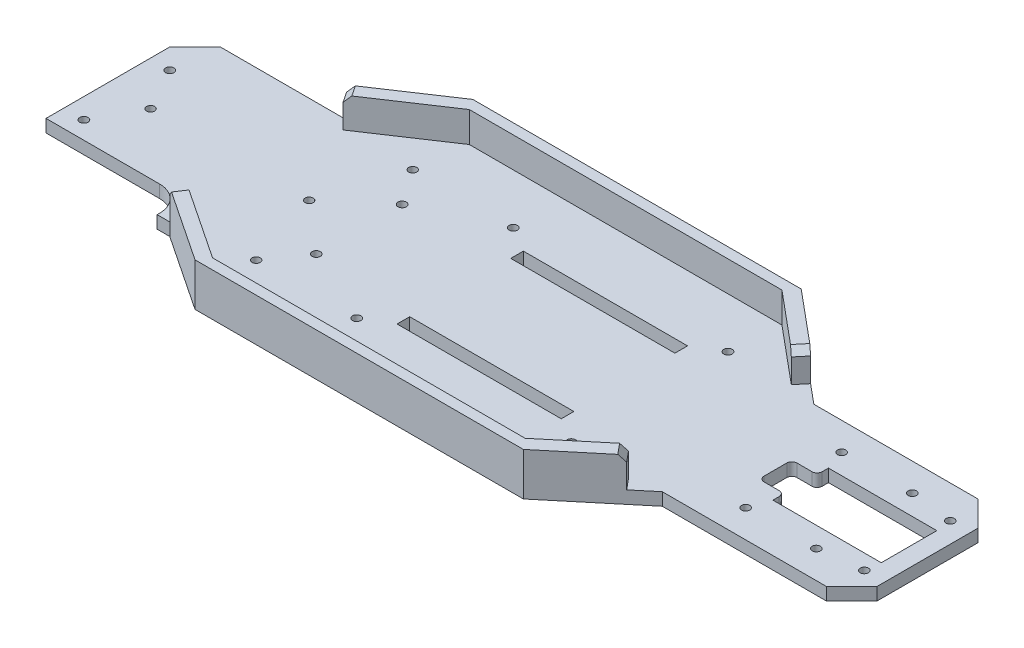
SolidWorks part; units mm, degrees
material "PETG - Polymaker"
ref_plane "Front Plane" through (0, 0, 0) normal (0, 0, 1) x (1, 0, 0)
ref_plane "Top Plane" through (0, 0, 0) normal (0, 1, 0) x (1, 0, 0)
ref_plane "Right Plane" through (0, 0, 0) normal (1, 0, 0) x (0, 0, -1)
sketch "Sketch1" plane through (0, 0, 0) normal (0, 1, 0) x (1, 0, 0)
  line L0 (-235.1499, 0) -> (235.1499, 0) construction
  line L1 (0, 0) -> (0, 52596.8311) construction
  line L2 (-95, 35) -> (-65, 55)
  line L3 (-65, 55) -> (65, 55)
  line L4 (-95, 35) -> (-155, 35)
  line L5 (-155, 35) -> (-155, -35)
  line L6 (-65, -55) -> (65, -55)
  line L7 (-95, -35) -> (-65, -55)
  line L8 (-95, -35) -> (-155, -35)
  line L9 (65, 55) -> (95, 30)
  line L10 (95, 30) -> (170, 30)
  line L11 (170, 30) -> (170, -30)
  line L12 (95, -30) -> (170, -30)
  line L13 (65, -55) -> (95, -30)
  point P3 (0, 0)
  point P10 (-80, 45)
  point P15 (-80, -45)
  point P18 (-155, 0)
  point P19 (0, -55)
  point P20 (0, 55)
  point P23 (170, 0)
  dimension "D1" = 55
  dimension "D2" = 70
  dimension "D3" = 30
  dimension "D4" = 60
  dimension "D5" = 130
  dimension "D6" = 75
  dimension "D7" = 60
  dimension "D8" = 30
  dimension "D9" = 110
extrude "Boss-Extrude1" add sketch "Sketch1" along normal blind 5
sketch "Sketch3" plane through (0, 5, 0) normal (0, 1, 0) x (1, 0, 0)
  line L0 (0, 0) -> (50000, 0) construction
  line L1 (0, 0) -> (0, 50000) construction
  line L2 (0, 55) -> (-65, 55)
  line L3 (65, 55) -> (-65, 55) construction
  line L4 (-65, 55) -> (-95, 35)
  line L5 (-95, 35) -> (-92.2265, 30.8397)
  line L6 (-92.2265, 30.8397) -> (-62.2265, 50.8397)
  line L7 (-62.2265, 50.8397) -> (0, 50.8397)
  line L8 (-65, 55) -> (-62.2265, 50.8397) construction
  line L9 (0, 55) -> (65, 55)
  line L10 (65, 55) -> (87.3178, 36.4018)
  line L11 (87.3178, 36.4018) -> (83.8509, 32.2416)
  line L12 (83.8509, 32.2416) -> (61.5331, 50.8397)
  line L13 (61.5331, 50.8397) -> (0, 50.8397)
  line L14 (61.5331, 50.8397) -> (65, 55) construction
  line L15 (61.5331, -50.8397) -> (65, -55) construction
  line L16 (-65, -55) -> (-62.2265, -50.8397) construction
  line L27 (-65, 55) -> (-95, 35) construction
  line L28 (95, 30) -> (65, 55) construction
  line L29 (61.5331, -50.8397) -> (0, -50.8397)
  line L30 (83.8509, -32.2416) -> (61.5331, -50.8397)
  line L31 (87.3178, -36.4018) -> (83.8509, -32.2416)
  line L32 (65, -55) -> (87.3178, -36.4018)
  line L33 (0, -55) -> (65, -55)
  line L34 (-62.2265, -50.8397) -> (0, -50.8397)
  line L35 (-92.2265, -30.8397) -> (-62.2265, -50.8397)
  line L36 (-95, -35) -> (-92.2265, -30.8397)
  line L37 (-65, -55) -> (-95, -35)
  line L38 (0, -55) -> (-65, -55)
  dimension "D1" = 5
  dimension "D2" = 0
  dimension "D3" = 10
extrude "Chassis-Walls1" add sketch "Sketch3" along normal blind 12
chamfer "Chamfer1" distance 10 angle 45 2 edges at (-155, 2.5, -35) (-155, 2.5, 35)
chamfer "Chamfer2" distance 10 angle 45 2 edges at (170, 2.5, -30) (170, 2.5, 30)
chamfer "Chamfer3" distance 2.5 angle 45 4 edges at (-93.6132, 17, -32.9199) (85.5843, 17, -34.3217) (-93.6132, 17, 32.9199) (85.5843, 17, 34.3217)
sketch "Sketch4" plane through (0, 0, 0) normal (0, -1, 0) x (1, 0, 0)
  line L0 (0, 0) -> (50000, 0) construction
  line L1 (-147, 17) -> (-55, 17) construction
  line L2 (-155, -25) -> (-155, 25) construction
  circle A0 centre (-147, 17) radius 1.65
  circle A1 centre (-55, 17) radius 1.65
  circle A2 centre (-55, -17) radius 1.65
  circle A3 centre (-147, -17) radius 1.65
  circle A4 centre (-25, 31) radius 1.65
  circle A5 centre (60, 31) radius 1.65
  circle A6 centre (60, -31) radius 1.65
  circle A7 centre (-25, -31) radius 1.65
  dimension "D1" = 3.3
  dimension "D2" = 3.3
  dimension "D6" = 3.3
  dimension "D8" = 3.3
  dimension "D3" = 8
  dimension "D4" = 92
  dimension "D5" = 34
  dimension "D7" = 30
  dimension "D9" = 85
  dimension "D10" = 62
extrude "Cut-Extrude1" cut sketch "Sketch4" against normal blind 10
sketch "Sketch5" plane through (0, 5, 0) normal (0, 1, 0) x (1, 0, 0)
  line L0 (-155, -24) -> (-100, -24)
  line L1 (-155, 25) -> (-155, -25) construction
  line L2 (-100, -24) -> (-100, -35)
  line L3 (-145, -35) -> (-95, -35) construction
  line L4 (-100, -35) -> (-155, -35)
  line L5 (-155, -35) -> (-155, -24)
  dimension "D1" = 55
  dimension "D2" = 11
extrude "Cut-Extrude2" cut sketch "Sketch5" against normal blind 10
sketch "Sketch6" plane through (0, 5, 0) normal (0, 1, 0) x (1, 0, 0)
  line L0 (0, 0) -> (50000, 0) construction
  line L1 (60, 31) -> (-25, 31) construction
  line L2 (17.5, 30.75) -> (17.5, 50030.75) construction
  line L3 (-15, -20) -> (50, -25) construction
  line L4 (-15, 25) -> (50, 25)
  line L5 (-15, 25) -> (-15, 20)
  line L6 (-15, 20) -> (50, 20)
  line L7 (50, 25) -> (50, 20)
  line L8 (-15, 25) -> (50, 20) construction
  line L9 (-15, 20) -> (50, 25) construction
  line L10 (-15, -25) -> (50, -20) construction
  line L11 (50, -25) -> (50, -20)
  line L12 (-15, -20) -> (50, -20)
  line L13 (-15, -25) -> (-15, -20)
  line L14 (-15, -25) -> (50, -25)
  point P9 (17.5, 31)
  point P10 (17.5, 22.5)
  point P19 (17.5, -22.5)
  dimension "D1" = 5
  dimension "D2" = 65
  dimension "D3" = 20
extrude "Cut-Extrude3" cut sketch "Sketch6" against normal through all
fillet "Fillet1" radius 10 1 edges at (-100, 2.5, 24)
sketch "Sketch7" plane through (0, 5, 0) normal (0, 1, 0) x (1, 0, 0)
  line L0 (175, 0) -> (50175, 0) construction
  line L1 (170, -20) -> (170, 20) construction
  line L3 (120.8, 10) -> (161.7, 10) construction
  line L4 (120.8, 10) -> (120.8, -10) construction
  line L5 (120.8, -10) -> (161.7, -10) construction
  line L6 (161.7, 10) -> (161.7, -10) construction
  line L7 (120.8, 10) -> (161.7, -10) construction
  line L8 (120.8, -10) -> (161.7, 10) construction
  line L9 (119.8, 11) -> (162.7, 11)
  line L10 (119.8, 11) -> (119.8, -11)
  line L11 (119.8, -11) -> (162.7, -11)
  line L12 (162.7, 11) -> (162.7, -11)
  line L13 (119.8, 11) -> (162.7, -11) construction
  line L14 (119.8, -11) -> (162.7, 11) construction
  point P4 (170, 0)
  point P5 (141.25, 0)
  point P10 (141.25, 0)
  dimension "D1" = 20
  dimension "D2" = 40.9
  dimension "D3" = 1
  dimension "D4" = 1
  dimension "D5" = 8.3
extrude "Cut-Extrude4" cut sketch "Sketch7" against normal through all
sketch "Sketch9" plane through (0, 5, 0) normal (0, 1, 0) x (1, 0, 0)
  circle A0 centre (117, -19) radius 1.625
  circle A1 centre (145, -19) radius 1.625
  circle A2 centre (162, -17) radius 1.625
  dimension "D1" = 3.25
  dimension "D2" = 3.25
  dimension "D3" = 3.25
extrude "Cut-Extrude5" cut sketch "Sketch9" against normal through all
mirror "Mirror1" about plane through (0, 0, 0) normal (0, 0, 1) of "Cut-Extrude5"
sketch "Sketch10" plane through (0, 5, 0) normal (0, 1, 0) x (1, 0, 0)
  line L0 (124.8, 0) -> (50124.8, 0) construction
  line L1 (119.8, 11) -> (119.8, -11) construction
  line L2 (119.8, 6.5) -> (109.8, 6.5)
  line L3 (109.8, 6.5) -> (109.8, -6.5)
  line L4 (119.8, 6.5) -> (119.8, -6.5)
  line L5 (119.8, -6.5) -> (109.8, -6.5)
  point P4 (119.8, 0)
  point P10 (119.8, 0)
  point P11 (109.8, 0)
  dimension "D1" = 13
  dimension "D2" = 10
extrude "Servo-Cable-Cutout" cut sketch "Sketch10" against normal blind 10
fillet "Fillet2" radius 2 4 edges at (119.8, 2.5, -6.5) (119.8, 2.5, 6.5) (109.8, 2.5, 6.5) (109.8, 2.5, -6.5)
sketch "Sketch11" plane through (0, 5, 0) normal (0, 1, 0) x (1, 0, 0)
  line L0 (-153, 11.5) -> (-153, -11.5) construction
  line L1 (-153, 0) -> (-122.2, 0) construction
  line L2 (-122.2, -11.5) -> (-122.2, 11.5) construction
  line L3 (-122.2, 0) -> (-47.5, 0) construction
  line L4 (-47.5, -12.0003) -> (-47.5, 9.9997) construction
  line L5 (-79.8, 9.5) -> (-79.8, -9.5) construction
  line L6 (-74.8, 0) -> (-74.8, 50000) construction
  line L7 (-25, 31) -> (-74.8, 31) construction
  circle A0 centre (-137.6, 0) radius 1.6
  circle A1 centre (-74.8, 0) radius 1.6
  circle A2 centre (-64.8, 31) radius 1.6
  circle A3 centre (-64.8, -31) radius 1.6
  point P27 (0, 0)
  dimension "D1" = 3.2
  dimension "D2" = 3.2
  dimension "D4" = 3.2
  dimension "D3" = 5
  dimension "D5" = 10
  dimension "D6" = 31
extrude "Cut-Extrude6" cut sketch "Sketch11" against normal through all
equation "\"D6@Sketch4\"=\"D2@Sketch4\""
equation "\"D8@Sketch4\"=\"D2@Sketch4\""
equation "\"D2@Sketch4\"=\"D1@Sketch4\""
equation "\"D2@Sketch9\"=\"D1@Sketch9\""
equation "\"D3@Sketch9\"=\"D1@Sketch9\""
equation "\"D4@Sketch11\"=\"D1@Sketch11\""
equation "\"D2@Sketch11\"=\"D1@Sketch11\""
